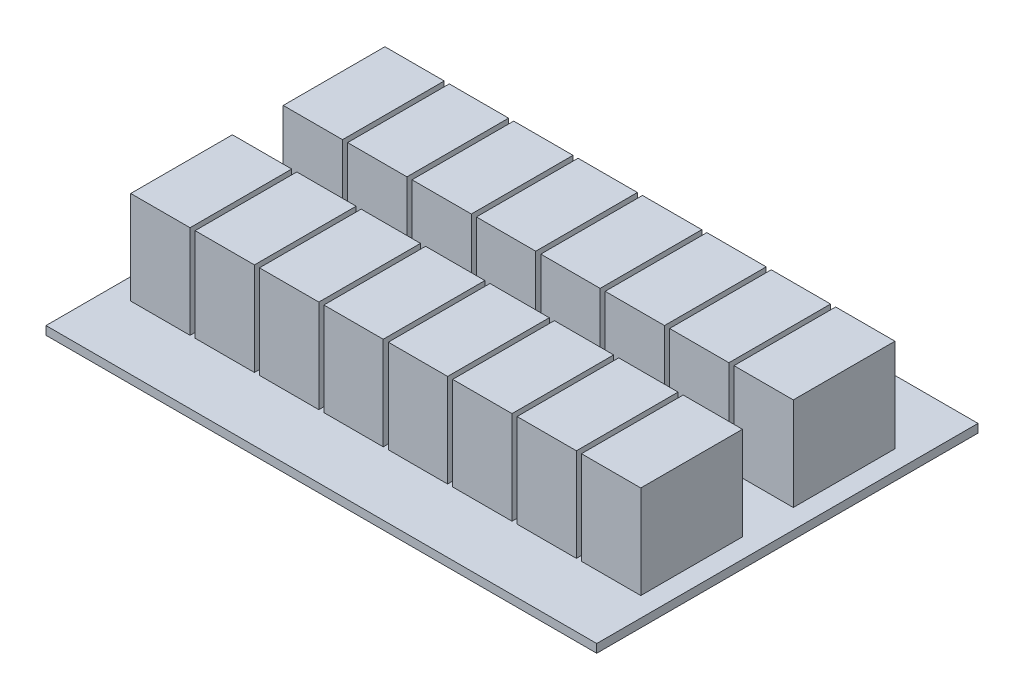
SolidWorks part; units mm, degrees
ref_plane "Front Plane" through (0, 0, 0) normal (0, 0, 1) x (1, 0, 0)
ref_plane "Top Plane" through (0, 0, 0) normal (0, 1, 0) x (1, 0, 0)
ref_plane "Right Plane" through (0, 0, 0) normal (1, 0, 0) x (0, 0, -1)
sketch "Sketch1" plane through (0, 0, 0) normal (0, 1, 0) x (1, 0, 0)
  line L1 (-65.7365, 64.6981) -> (99.3635, 64.6981)
  line L2 (-65.7365, 64.6981) -> (-65.7365, -49.6019)
  line L3 (-65.7365, -49.6019) -> (99.3635, -49.6019)
  line L4 (99.3635, 64.6981) -> (99.3635, -49.6019)
  dimension "D1" = 165.1
  dimension "D2" = 114.3
extrude "Boss-Extrude1" add sketch "Sketch1" along normal blind 2.54
sketch "Sketch2" plane through (0, 2.54, 0) normal (0, 1, 0) x (1, 0, 0)
  line L0 (56.4375, 15.1681) -> (74.2175, 15.1681)
  line L1 (75.7415, 45.6481) -> (93.5215, 45.6481)
  line L2 (75.7415, 45.6481) -> (75.7415, 15.1681)
  line L3 (75.7415, 15.1681) -> (93.5215, 15.1681)
  line L4 (93.5215, 45.6481) -> (93.5215, 15.1681)
  line L5 (56.4375, 45.6481) -> (56.4375, 15.1681)
  line L6 (56.4375, 45.6481) -> (74.2175, 45.6481)
  line L7 (74.2175, 45.6481) -> (74.2175, 15.1681)
  line L8 (37.1335, 15.1681) -> (54.9135, 15.1681)
  line L9 (37.1335, 45.6481) -> (37.1335, 15.1681)
  line L10 (37.1335, 45.6481) -> (54.9135, 45.6481)
  line L11 (54.9135, 45.6481) -> (54.9135, 15.1681)
  line L12 (17.8295, 15.1681) -> (35.6095, 15.1681)
  line L13 (17.8295, 45.6481) -> (17.8295, 15.1681)
  line L14 (17.8295, 45.6481) -> (35.6095, 45.6481)
  line L15 (35.6095, 45.6481) -> (35.6095, 15.1681)
  line L16 (-1.4745, 15.1681) -> (16.3055, 15.1681)
  line L17 (-1.4745, 45.6481) -> (-1.4745, 15.1681)
  line L18 (-1.4745, 45.6481) -> (16.3055, 45.6481)
  line L19 (16.3055, 45.6481) -> (16.3055, 15.1681)
  line L20 (-20.7785, 15.1681) -> (-2.9985, 15.1681)
  line L21 (-20.7785, 45.6481) -> (-20.7785, 15.1681)
  line L22 (-20.7785, 45.6481) -> (-2.9985, 45.6481)
  line L23 (-2.9985, 45.6481) -> (-2.9985, 15.1681)
  line L24 (-40.0825, 15.1681) -> (-22.3025, 15.1681)
  line L25 (-40.0825, 45.6481) -> (-40.0825, 15.1681)
  line L26 (-40.0825, 45.6481) -> (-22.3025, 45.6481)
  line L27 (-22.3025, 45.6481) -> (-22.3025, 15.1681)
  line L28 (-59.3865, 15.1681) -> (-41.6065, 15.1681)
  line L29 (-59.3865, 45.6481) -> (-59.3865, 15.1681)
  line L30 (-59.3865, 45.6481) -> (-41.6065, 45.6481)
  line L31 (-41.6065, 45.6481) -> (-41.6065, 15.1681)
  line L32 (56.4375, -30.5519) -> (74.2175, -30.5519)
  line L33 (56.4375, -0.0719) -> (56.4375, -30.5519)
  line L34 (56.4375, -0.0719) -> (74.2175, -0.0719)
  line L35 (74.2175, -0.0719) -> (74.2175, -30.5519)
  line L36 (37.1335, -30.5519) -> (54.9135, -30.5519)
  line L37 (37.1335, -0.0719) -> (37.1335, -30.5519)
  line L38 (37.1335, -0.0719) -> (54.9135, -0.0719)
  line L39 (54.9135, -0.0719) -> (54.9135, -30.5519)
  line L40 (17.8295, -30.5519) -> (35.6095, -30.5519)
  line L41 (17.8295, -0.0719) -> (17.8295, -30.5519)
  line L42 (17.8295, -0.0719) -> (35.6095, -0.0719)
  line L43 (35.6095, -0.0719) -> (35.6095, -30.5519)
  line L44 (-1.4745, -30.5519) -> (16.3055, -30.5519)
  line L45 (-1.4745, -0.0719) -> (-1.4745, -30.5519)
  line L46 (-1.4745, -0.0719) -> (16.3055, -0.0719)
  line L47 (16.3055, -0.0719) -> (16.3055, -30.5519)
  line L48 (-20.7785, -30.5519) -> (-2.9985, -30.5519)
  line L49 (-20.7785, -0.0719) -> (-20.7785, -30.5519)
  line L50 (-20.7785, -0.0719) -> (-2.9985, -0.0719)
  line L51 (-2.9985, -0.0719) -> (-2.9985, -30.5519)
  line L52 (-40.0825, -30.5519) -> (-22.3025, -30.5519)
  line L53 (-40.0825, -0.0719) -> (-40.0825, -30.5519)
  line L54 (-40.0825, -0.0719) -> (-22.3025, -0.0719)
  line L55 (-22.3025, -0.0719) -> (-22.3025, -30.5519)
  line L56 (-59.3865, -30.5519) -> (-41.6065, -30.5519)
  line L57 (-59.3865, -0.0719) -> (-59.3865, -30.5519)
  line L58 (-59.3865, -0.0719) -> (-41.6065, -0.0719)
  line L59 (-41.6065, -0.0719) -> (-41.6065, -30.5519)
  line L60 (75.7415, -30.5519) -> (93.5215, -30.5519)
  line L61 (75.7415, -0.0719) -> (75.7415, -30.5519)
  line L62 (75.7415, -0.0719) -> (93.5215, -0.0719)
  line L63 (93.5215, -0.0719) -> (93.5215, -30.5519)
  line L64 (99.3635, -49.6019) -> (99.3635, 64.6981) construction
  line L65 (-65.7365, -49.6019) -> (99.3635, -49.6019) construction
  line L66 (99.3635, 64.6981) -> (-65.7365, 64.6981) construction
  dimension "D1" = 30.48
  dimension "D2" = 17.78
  dimension "D5" = 5.842
  dimension "D6" = 19.05
  dimension "D7" = 19.05
  dimension "D3" = 8
  dimension "D4" = 2
extrude "Boss-Extrude2" add sketch "Sketch2" along normal blind 27.94
